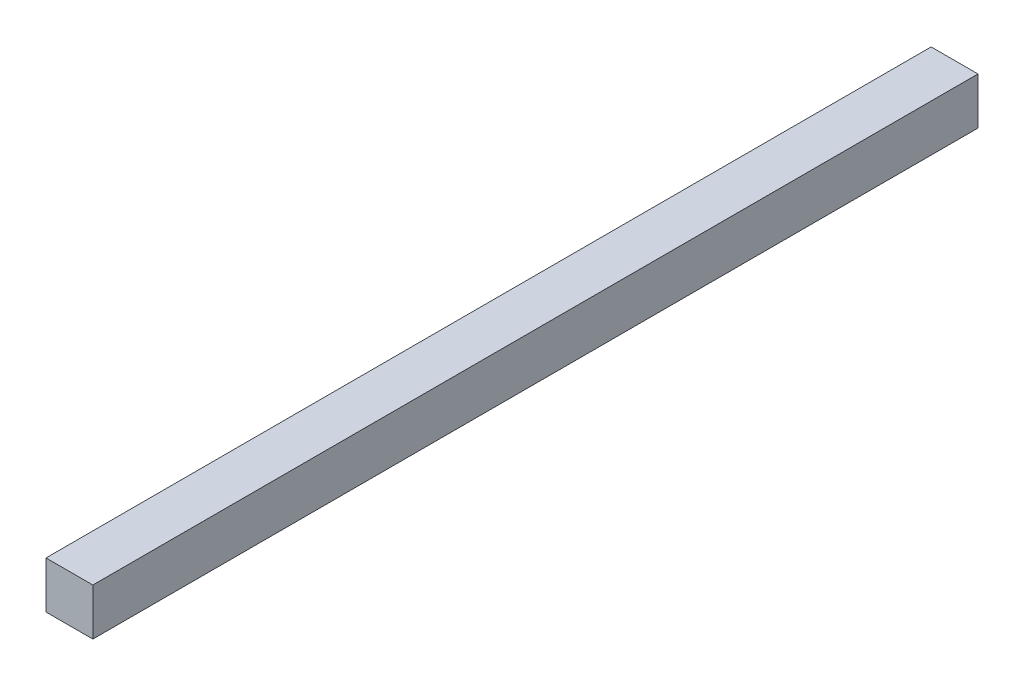
SolidWorks part; units mm, degrees
ref_plane "Face" through (0, 0, 0) normal (0, 0, 1) x (1, 0, 0)
ref_plane "Dessus" through (0, 0, 0) normal (0, 1, 0) x (1, 0, 0)
ref_plane "Droite" through (0, 0, 0) normal (1, 0, 0) x (0, 0, -1)
sketch "Esquisse1" plane through (0, 0, 0) normal (0, 0, 1) x (1, 0, 0)
  line L1 (0, 0) -> (18, 0)
  line L2 (0, 0) -> (0, 18)
  line L3 (0, 18) -> (18, 18)
  line L4 (18, 0) -> (18, 18)
  dimension "D1" = 18
  dimension "D2" = 18
extrude "Extrusion1" add sketch "Esquisse1" against normal blind 340
